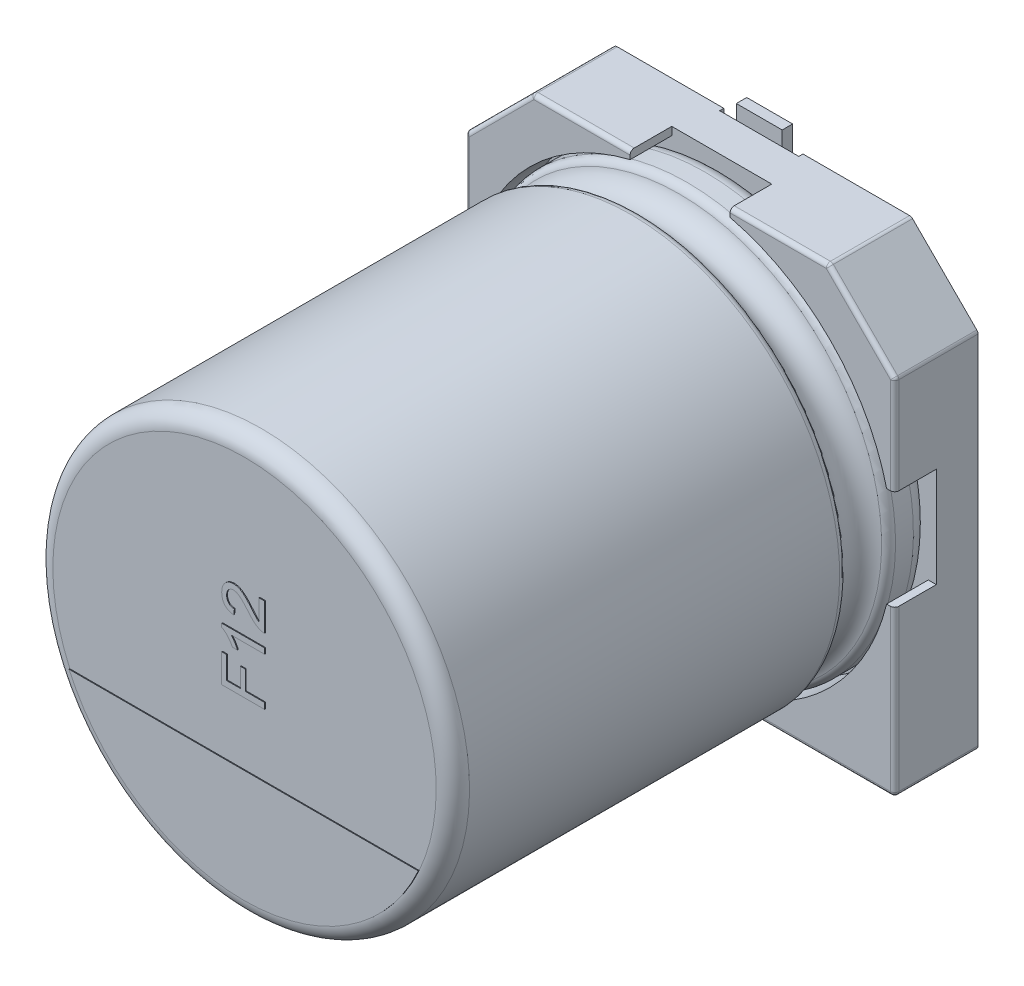
SolidWorks part; units mm, degrees
ref_plane "Plan de face" through (0, 0, 0) normal (0, 0, 1) x (1, 0, 0)
ref_plane "Plan de dessus" through (0, 0, 0) normal (0, 1, 0) x (1, 0, 0)
ref_plane "Plan de droite" through (0, 0, 0) normal (1, 0, 0) x (0, 0, -1)
sketch "Sketch2" plane through (0, 0, 0) normal (0, 0, 1) x (1, 0, 0)
  line L0 (-5.15, 3.55) -> (-3.55, 5.15)
  line L1 (-3.55, 5.15) -> (3.55, 5.15)
  line L2 (-5.15, 3.55) -> (-5.15, -5.15)
  line L3 (-5.15, -5.15) -> (5.15, -5.15)
  line L4 (5.15, 3.55) -> (5.15, -5.15)
  line L5 (-5.15, 5.15) -> (5.15, -5.15) construction
  line L6 (-5.15, -5.15) -> (5.15, 5.15) construction
  line L7 (3.55, 5.15) -> (5.15, 3.55)
  point P0 (0, 0)
  dimension "D1" = 10.3
  dimension "D2" = 10.3
extrude "Boss-Extrude1" add sketch "Sketch2" along normal blind 1
sketch "Sketch4" plane through (0, 0, 1) normal (0, 0, 1) x (1, 0, 0)
  line L0 (-5.15, 3.55) -> (-3.55, 5.15)
  line L1 (-3.55, 5.15) -> (-1.2, 5.15)
  line L3 (-5.15, 1.2) -> (-5.15, 3.55)
  line L4 (3.55, 5.15) -> (5.15, 3.55)
  line L5 (5.15, 3.55) -> (5.15, 1.2)
  line L6 (5.15, -5.15) -> (5.15, 3.55) construction
  line L7 (3.55, 5.15) -> (-3.55, 5.15) construction
  line L8 (1.2, 5.15) -> (3.55, 5.15)
  line L9 (-5.15, -5.15) -> (5.15, -5.15) construction
  line L10 (5.15, -1.2) -> (5.15, -5.15)
  line L11 (5.15, -5.15) -> (1.2, -5.15)
  line L12 (-5.15, -1.2) -> (-5.15, -5.15)
  line L13 (-5.15, -5.15) -> (-1.2, -5.15)
  line L14 (-4.946, -1.2) -> (4.946, -1.2) construction
  line L15 (-4.8253, 1.2) -> (5.0249, 1.2) construction
  line L16 (4.9568, 1.2) -> (5.15, 1.2)
  line L17 (4.9568, -1.2) -> (5.15, -1.2)
  line L18 (-4.9568, -1.2) -> (-5.15, -1.2)
  line L19 (-4.9568, 1.2) -> (-5.15, 1.2)
  line L20 (-1.2, 5.0139) -> (-1.2, -5.2906) construction
  line L21 (1.2, 5.0139) -> (1.2, -5.4) construction
  line L22 (-1.2, 5.15) -> (-1.2, 4.9568)
  line L23 (1.2, 5.15) -> (1.2, 4.9568)
  line L24 (-1.2, -4.9568) -> (-1.2, -5.15)
  line L25 (1.2, -4.9568) -> (1.2, -5.15)
  arc A0 (-1.2, 4.9568) -> (-4.9568, 1.2) centre (0, 0) ccw construction
  arc A1 (-4.9568, 1.2) -> (-1.2, 4.9568) centre (0, 0) cw
  arc A2 (1.2, 4.9568) -> (4.9568, 1.2) centre (0, 0) cw
  arc A3 (1.2, -4.9568) -> (4.9568, -1.2) centre (0, 0) ccw
  arc A4 (-1.2, -4.9568) -> (-4.9568, -1.2) centre (0, 0) cw
  arc A5 (4.9568, 1.2) -> (1.2, 4.9568) centre (0, 0) ccw construction
  arc A6 (1.2, -4.9568) -> (4.9568, -1.2) centre (0, 0) ccw construction
  arc A7 (-4.9568, -1.2) -> (-1.2, -4.9568) centre (0, 0) ccw construction
  point P33 (0, -1.2)
  dimension "D1" = 10.2
  dimension "D2" = 1.2
  dimension "D3" = 1.2
  dimension "D4" = 1.2
  dimension "D5" = 1.2
sketch "Sketch5" plane through (0, 0, 0) normal (0, 0, 1) x (1, 0, 0)
extrude "Boss-Extrude2" add sketch "Sketch4" along normal blind 1
sketch "Sketch7" plane through (0, 0, 0) normal (0, 0, -1) x (1, 0, 0)
  line L1 (-3.5816, 3.5474) -> (3.5816, 3.5474) construction
  line L2 (-3.5816, 3.5474) -> (-3.5816, -3.5474) construction
  line L3 (-3.5816, -3.5474) -> (3.5816, -3.5474) construction
  line L4 (3.5816, 3.5474) -> (3.5816, -3.5474) construction
  line L5 (-3.5816, 3.5474) -> (3.5816, -3.5474) construction
  line L6 (-3.5816, -3.5474) -> (3.5816, 3.5474) construction
  circle A0 centre (-3.5816, 3.5474) radius 0.35
  circle A1 centre (3.5816, 3.5474) radius 0.35
  circle A2 centre (-3.5816, -3.5474) radius 0.35
  circle A3 centre (3.5816, -3.5474) radius 0.35
  point P0 (0, 0)
  dimension "D1" = 0.7
  dimension "D2" = 0.7
  dimension "D3" = 0.7
  dimension "D4" = 0.7
extrude "Spacer Pad" add sketch "Sketch7" along normal blind 0.15
sketch "Sketch8" plane through (0, 0, 0) normal (0, 0, -1) x (1, 0, 0)
  line L0 (-0.95, 4.3618) -> (-0.95, -4.4479) construction
  line L1 (0.95, 4.3618) -> (0.95, -4.4479) construction
  dimension "D1" = 0.95
  dimension "D2" = 1.9
sketch "Sketch9" plane through (0, 0, 0) normal (0, 0, -1) x (1, 0, 0)
  line L0 (-4.6239, -2.1) -> (5.0007, -2.1) construction
  line L1 (-4.6239, 2.1) -> (5.2975, 2.1) construction
  line L2 (-0.95, 4.3618) -> (-0.95, -4.4479) construction
  line L3 (-0.95, 2.1) -> (0.95, 2.1)
  line L4 (-0.95, 2.1) -> (-0.95, 5.15)
  line L5 (-0.95, 5.15) -> (0.95, 5.15)
  line L6 (0.95, 2.1) -> (0.95, 5.15)
  line L7 (0.95, 4.3618) -> (0.95, -4.4479) construction
  line L8 (-5.15, 5.15) -> (5.15, 5.15) construction
  line L9 (3.55, -5.15) -> (-3.55, -5.15) construction
  line L10 (-0.95, -2.1) -> (0.95, -2.1)
  line L11 (-0.95, -2.1) -> (-0.95, -5.15)
  line L12 (-0.95, -5.15) -> (0.95, -5.15)
  line L13 (0.95, -2.1) -> (0.95, -5.15)
  dimension "D1" = 2.1
  dimension "D2" = 2.1
extrude "Cut-Extrude1" cut sketch "Sketch9" against normal blind 0.1
fillet "Fillet1" radius 0.1 6 edges at (-5.15, 3.55, 1) (-3.55, 5.15, 1) (3.55, 5.15, 1) (5.15, 3.55, 1) (5.15, -5.15, 1) (-5.15, -5.15, 1)
sketch "Sketch10" plane through (0, 0, 0) normal (1, 0, 0) x (0, 0, -1)
  line L0 (18.9631, 0) -> (-18.9631, 0) construction
  line L2 (-12.4536, 0) -> (-12.4536, 4.6)
  line L3 (-12.0536, 5) -> (-3.1708, 5)
  line L4 (-1, 4.6) -> (-1, 0)
  line L7 (-1.8292, 5) -> (-1.4, 5)
  arc A0 (-12.4536, 4.6) -> (-12.0536, 5) centre (-12.0536, 4.6) cw
  arc A1 (-1.4, 5) -> (-1, 4.6) centre (-1.4, 4.6) cw
  arc A2 (-2.9792, 4.8571) -> (-2.0208, 4.8571) centre (-2.5, 5) ccw
  arc A3 (-3.1708, 5) -> (-2.9792, 4.8571) centre (-3.1708, 4.8) cw
  arc A4 (-2.0208, 4.8571) -> (-1.8292, 5) centre (-1.8292, 4.8) cw
  point P4 (0, 1)
  point P13 (-12.4536, 5)
  dimension "D2" = 0.4
  dimension "D3" = 0.4
  dimension "D4" = 0.2
  dimension "D1" = 5
revolve "Revolve1" add sketch "Sketch10" angle 360 about L0
fillet "Fillet2" radius 0.1 16 edges at (3.125, -5.15, 2) (5.1207, -5.1207, 2) (5.15, 2.3543, 2) (5.1424, 3.5468, 2) (2.3543, 5.15, 2) (3.5468, 5.1424, 2) (-2.3543, 5.15, 2) (-3.5468, 5.1424, 2) (-4.35, 4.35, 2) (-5.1424, 3.5468, 2) (-5.15, -3.125, 2) (-5.1207, -5.1207, 2) (5.15, -3.125, 2) (4.35, 4.35, 2) (-5.15, 2.3543, 2) (-3.125, -5.15, 2)
sketch "Sketch13" plane through (0, 0, 12.4536) normal (0, 0, 1) x (1, 0, 0)
  line L0 (-6.1745, -1.8934) -> (2.8059, -1.8934) construction
  line L1 (-4.1923, -1.8934) -> (4.1923, -1.8934)
  arc A0 (4.1923, -1.8934) -> (-4.1923, -1.8934) centre (0, 0) cw
  point P3 (-1.6843, -1.8934)
extrude "Cathode marker" add sketch "Sketch13" along normal blind 0.02
sketch "Sketch15" plane through (0, 0, 12.4536) normal (0, 0, 1) x (1, 0, 0)
  line L1 (0.5, 2.1812) -> (0.5, -0.5) construction
  text T1 "F12" font "Arial" height in points 4
extrude "Text" add sketch "Sketch15" along normal blind 0.02
sketch "Sketch18" plane through (0, 0, 0.1) normal (0, 0, -1) x (1, 0, 0)
  line L0 (0, 5.1012) -> (0, -5.1012) construction
  point P4 (0, 0)
sketch "Sketch19" plane through (0, 0, 0.1) normal (0, 0, -1) x (1, 0, 0)
  line L0 (-1.0534, -5.5) -> (1.0534, -5.5) construction
  line L2 (-0.95, -5.15) -> (0.95, -5.15) construction
  line L3 (-1.9391, 5.5) -> (1.9391, 5.5) construction
  line L5 (0.95, 5.15) -> (-0.95, 5.15) construction
  line L6 (0, 5.1012) -> (0, -5.1012) construction
  line L7 (-0.55, 2.3) -> (0.55, 2.3)
  line L8 (-0.55, 2.3) -> (-0.55, 5.5)
  line L9 (-0.55, 5.5) -> (0.55, 5.5)
  line L10 (0.55, 2.3) -> (0.55, 5.5)
  line L11 (-0.55, 2.3) -> (0.55, 5.5) construction
  line L12 (-0.55, 5.5) -> (0.55, 2.3) construction
  line L14 (-0.55, -2.3) -> (0.55, -2.3)
  line L15 (-0.55, -2.3) -> (-0.55, -5.5)
  line L16 (-0.55, -5.5) -> (0.55, -5.5)
  line L17 (0.55, -2.3) -> (0.55, -5.5)
  line L18 (-0.55, -2.3) -> (0.55, -5.5) construction
  line L19 (-0.55, -5.5) -> (0.55, -2.3) construction
  point P3 (0, -5.5)
  point P8 (0, 5.5)
  point P10 (0, 3.9)
  point P17 (0, -3.9)
  dimension "D1" = 0.35
  dimension "D2" = 0.35
  dimension "D3" = 1.1
  dimension "D4" = 3.2
  dimension "D5" = 1.1
  dimension "D6" = 3.2
extrude "Boss-Extrude6" add sketch "Sketch19" along normal blind 0.25
